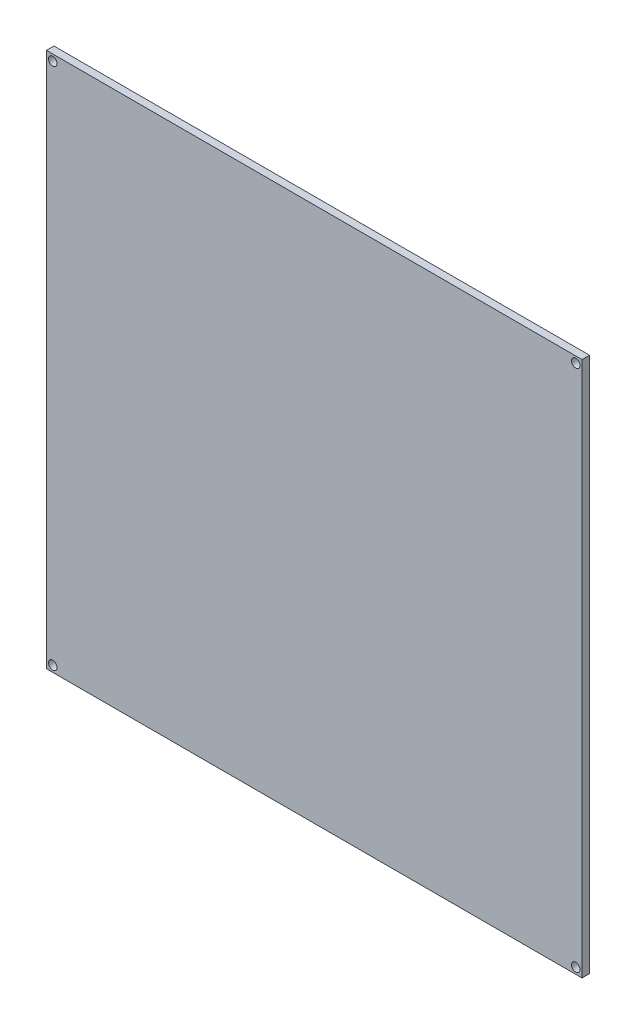
SolidWorks part; units mm, degrees
material "A-Fibra di vetro"
ref_plane "Piano frontale" through (0, 0, 0) normal (0, 0, 1) x (1, 0, 0)
ref_plane "Piano superiore" through (0, 0, 0) normal (0, 1, 0) x (1, 0, 0)
ref_plane "Piano destro" through (0, 0, 0) normal (1, 0, 0) x (0, 0, -1)
sketch "Schizzo1" plane through (0, 0, 0) normal (0, 0, 1) x (1, 0, 0)
  line L0 (-214, 214) -> (0, 0) construction
  line L1 (0, 0) -> (-214, 0)
  line L2 (0, 0) -> (0, 214)
  line L3 (0, 214) -> (-214, 214)
  line L4 (-214, 0) -> (-214, 214)
  line L5 (-214, 0) -> (0, 214) construction
extrude "Estrusione-Estrusione1" add sketch "Schizzo1" against normal blind 3
hole_wizard "Foro per Vite M3-1" positions "Schizzo3" profile "Schizzo2" hole size "M3" standard "ISO" end condition up to next
sketch "Schizzo3" plane through (0, 0, 0) normal (0, 0, 1) x (1, 0, 0)
  line L0 (0, 214) -> (-214, 0) construction
  line L2 (0, 0) -> (-214, 214) construction
  point P0 (-2.5, 211.5)
  point P2 (-2.5, 2.5)
  point P4 (-211.5, 211.5)
  point P6 (-211.5, 2.5)
  dimension "D1" = 209
  dimension "D2" = 209
sketch "Schizzo2" plane through (-2.5, 211.5, 0) normal (1, 0, 0) x (0, -1, 0)
  line L0 (0, 0) -> (0, 3)
  line L1 (0, 3) -> (1.7, 3)
  line L2 (1.7, 3) -> (1.7, 0)
  line L5 (1.7, 0) -> (0, 0)
  line L11 (0, -6.35) -> (0, 107.95) construction
  dimension "Thru Hole Dia." = 3.4
  dimension "Thru Hole Depth" = 3
